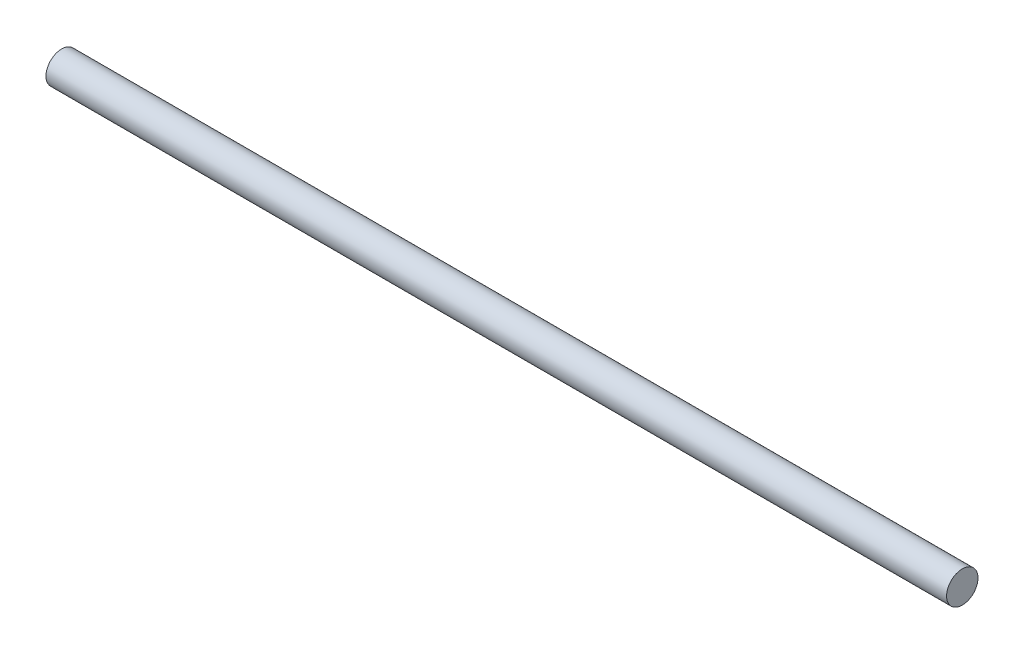
SolidWorks part; units mm, degrees
ref_plane "Front Plane" through (0, 0, 0) normal (0, 0, 1) x (1, 0, 0)
ref_plane "Top Plane" through (0, 0, 0) normal (0, 1, 0) x (1, 0, 0)
ref_plane "Right Plane" through (0, 0, 0) normal (1, 0, 0) x (0, 0, -1)
sketch "Sketch1" plane through (0, 0, 0) normal (1, 0, 0) x (0, 0, -1)
  circle A0 centre (0, 0) radius 5
  dimension "D1" = 10
extrude "Boss-Extrude1" add sketch "Sketch1" along normal mid plane 286.6
